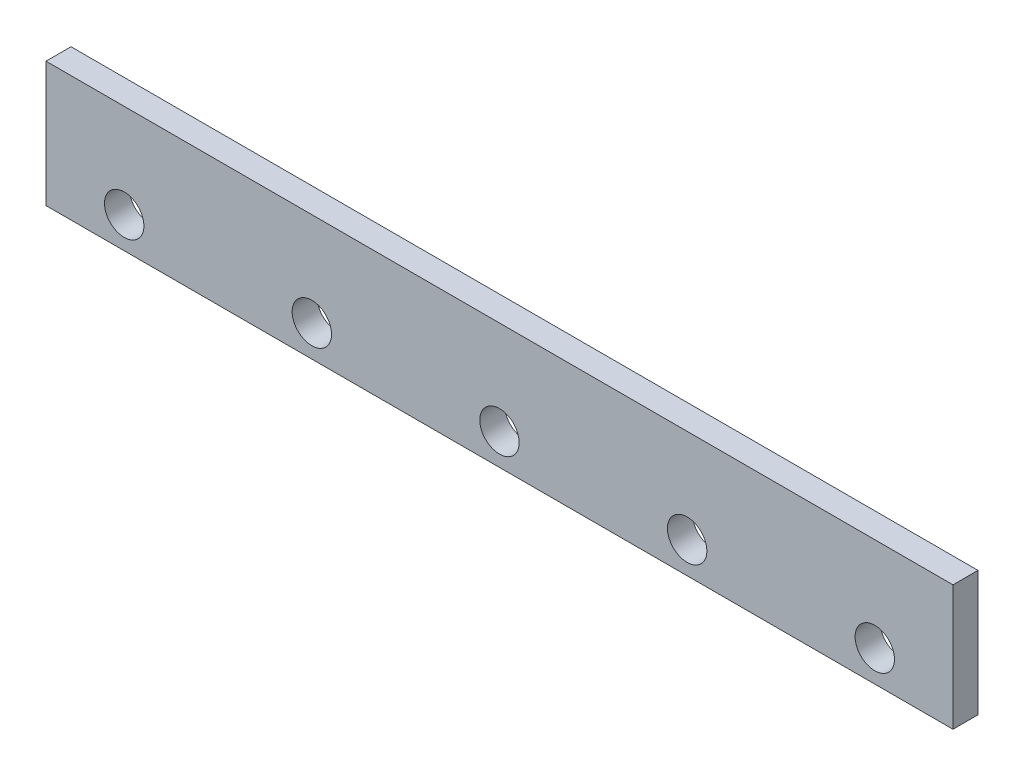
SolidWorks part; units mm, degrees
ref_plane "Alzado" through (0, 0, 0) normal (0, 0, 1) x (1, 0, 0)
ref_plane "Planta" through (0, 0, 0) normal (0, 1, 0) x (1, 0, 0)
ref_plane "Vista lateral" through (0, 0, 0) normal (1, 0, 0) x (0, 0, -1)
sketch "Croquis1" plane through (0, 0, 0) normal (0, 0, 1) x (1, 0, 0)
  line L1 (-290, -40) -> (290, -40)
  line L2 (-290, -40) -> (-290, 40)
  line L3 (-290, 40) -> (290, 40)
  line L4 (290, -40) -> (290, 40)
  line L5 (-290, -40) -> (290, 40) construction
  line L6 (-290, 40) -> (290, -40) construction
  circle A0 centre (-240, -20) radius 12.6
  circle A1 centre (-120, -20) radius 12.6
  circle A2 centre (0, -20) radius 12.6
  circle A3 centre (120, -20) radius 12.6
  circle A4 centre (240, -20) radius 12.6
  point P0 (0, 0)
  dimension "D5" = 25.2
  dimension "D1" = 580
  dimension "D2" = 80
  dimension "D3" = 50
  dimension "D4" = 20
  dimension "D7" = 50
  dimension "D6" = 5
extrude "Saliente-Extruir1" add sketch "Croquis1" against normal blind 16
